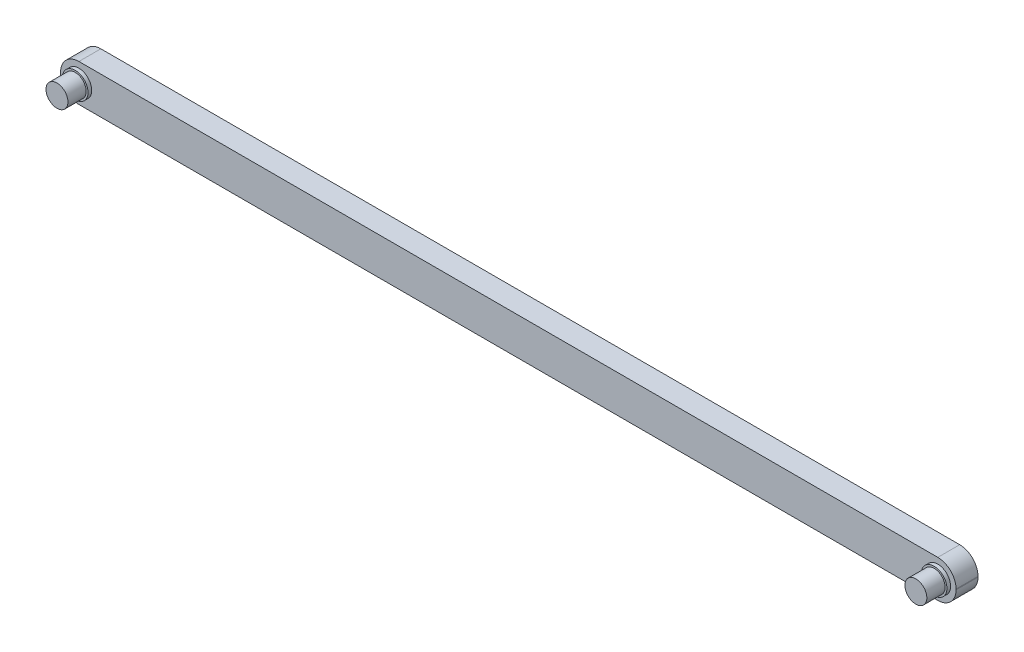
SolidWorks part; units mm, degrees
ref_plane "Front Plane" through (0, 0, 0) normal (0, 0, 1) x (1, 0, 0)
ref_plane "Top Plane" through (0, 0, 0) normal (0, 1, 0) x (1, 0, 0)
ref_plane "Right Plane" through (0, 0, 0) normal (1, 0, 0) x (0, 0, -1)
sketch "Sketch1" plane through (0, 0, 0) normal (0, 0, 1) x (1, 0, 0)
  line L1 (-61.25, 5.0994) -> (61.25, 5.0994)
  line L2 (-61.25, 5.0994) -> (-61.25, -5.0994)
  line L3 (-61.25, -5.0994) -> (61.25, -5.0994)
  line L4 (61.25, 5.0994) -> (61.25, -5.0994)
  line L5 (-61.25, 5.0994) -> (61.25, -5.0994) construction
  line L6 (-61.25, -5.0994) -> (61.25, 5.0994) construction
  point P0 (0, 0)
  dimension "D1" = 122.5
  dimension "D2" = 10.1989
extrude "Boss-Extrude1" add sketch "Sketch1" along normal blind 6
fillet "Fillet1" radius 5 2 edges at (61.25, -5.0994, 3) (61.25, 5.0994, 3)
sketch "Sketch2" plane through (0, 0, 6) normal (0, 0, 1) x (1, 0, 0)
  line L0 (61.25, 0) -> (132.9336, 0) construction
  line L1 (61.25, -0.0994) -> (61.25, 0.0994) construction
  circle A0 centre (56.25, 0) radius 3.5
  dimension "D2" = 7
  dimension "D1" = 5
extrude "Boss-Extrude2" add sketch "Sketch2" along normal blind 1
sketch "Sketch3" plane through (0, 0, 7) normal (0, 0, 1) x (1, 0, 0)
  circle A0 centre (56.25, 0) radius 3
  circle A1 centre (56.25, 0) radius 3.5 construction
  dimension "D1" = 6
extrude "Boss-Extrude3" add sketch "Sketch3" along normal blind 5
mirror "Mirror1" about plane through (-61.25, 5.0994, 6) normal (1, 0, 0) of "Boss-Extrude1", "Fillet1", "Boss-Extrude2", "Boss-Extrude3"
